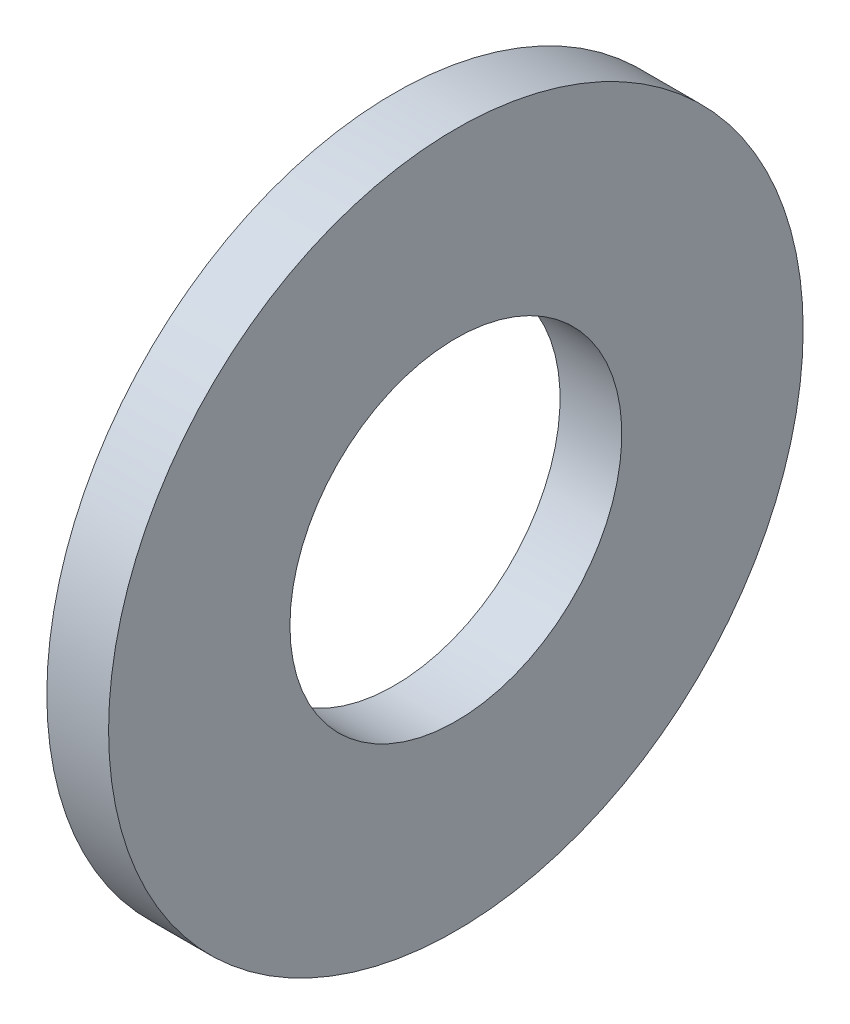
SolidWorks part; units mm, degrees
ref_plane "Plane1" through (0, 0, 0) normal (0, 0, 1) x (1, 0, 0)
ref_plane "Plane2" through (0, 0, 0) normal (0, 1, 0) x (1, 0, 0)
ref_plane "Plane3" through (0, 0, 0) normal (1, 0, 0) x (0, 0, -1)
sketch "Sketch1" plane through (0, 0, 0) normal (0, 0, 1) x (1, 0, 0)
  line L0 (-34.925, 0) -> (9.525, 0) construction
  line L1 (0, 2.15) -> (0, 4.5)
  line L2 (0, 4.5) -> (-0.8, 4.5)
  line L3 (-0.8, 4.5) -> (-0.8, 2.15)
  line L4 (-0.8, 2.15) -> (0, 2.15)
  dimension "Thickness" = 0.8
  dimension "Inside_dia" = 4.3
  dimension "Outside_dia" = 9
revolve "Base-Revolve" add sketch "Sketch1" angle 360 about L0
